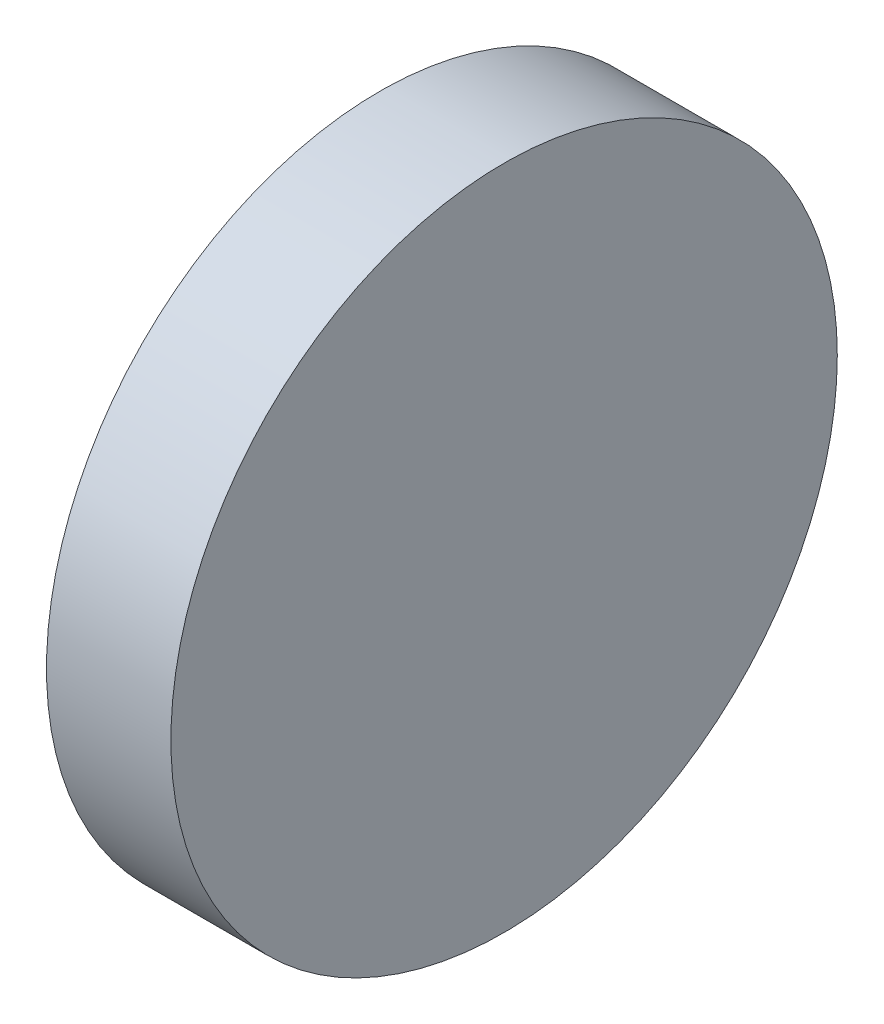
SolidWorks part; units mm, degrees
ref_plane "Front Plane" through (0, 0, 0) normal (0, 0, 1) x (1, 0, 0)
ref_plane "Top Plane" through (0, 0, 0) normal (0, 1, 0) x (1, 0, 0)
ref_plane "Right Plane" through (0, 0, 0) normal (1, 0, 0) x (0, 0, -1)
sketch "Sketch1" plane through (0, 0, 0) normal (1, 0, 0) x (0, 0, -1)
  circle A0 centre (0, 0) radius 37.5
  dimension "D1" = 75
extrude "Boss-Extrude1" add sketch "Sketch1" along normal mid plane 14
